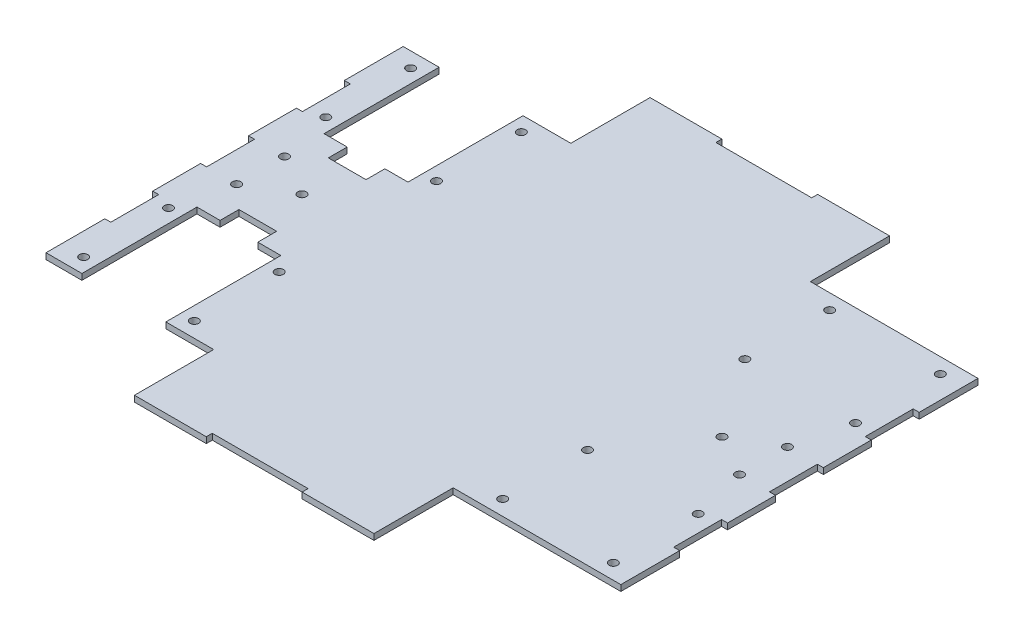
SolidWorks part; units mm, degrees
ref_plane "Front Plane" through (0, 0, 0) normal (0, 0, 1) x (1, 0, 0)
ref_plane "Top Plane" through (0, 0, 0) normal (0, 1, 0) x (1, 0, 0)
ref_plane "Right Plane" through (0, 0, 0) normal (1, 0, 0) x (0, 0, -1)
sketch "Sketch1" plane through (0, 0, 0) normal (0, 1, 0) x (1, 0, 0)
  line L0 (152.4, 94.7) -> (63.5, 94.7)
  line L1 (-152.4, -136.7) -> (152.4, -136.7)
  line L2 (-152.4, -136.7) -> (-152.4, 136.7)
  line L3 (-152.4, 136.7) -> (152.4, 136.7)
  line L4 (152.4, -136.7) -> (152.4, 136.7)
  line L5 (-152.4, -136.7) -> (152.4, 136.7) construction
  line L6 (-152.4, 136.7) -> (152.4, -136.7) construction
  line L7 (63.5, 94.7) -> (63.5, 136.7)
  line L8 (-152.4, 94.7) -> (-63.5, 94.7)
  line L9 (-63.5, 94.7) -> (-63.5, 136.7)
  line L10 (-152.4, -94.7) -> (-63.5, -94.7)
  line L11 (-63.5, -94.7) -> (-63.5, -136.7)
  line L12 (152.4, -94.7) -> (63.5, -94.7)
  line L13 (63.5, -94.7) -> (63.5, -136.7)
  line L14 (-88.8476, 33.7) -> (88.8476, 33.7) construction
  line L15 (88.8476, 33.7) -> (133.35, 33.7)
  line L16 (88.8476, 33.7) -> (88.8476, 94.7)
  line L17 (88.8476, 94.7) -> (133.35, 94.7)
  line L18 (133.35, 33.7) -> (133.35, 94.7)
  line L19 (88.8476, 33.7) -> (133.35, 94.7) construction
  line L20 (88.8476, 94.7) -> (133.35, 33.7) construction
  line L21 (88.8476, -33.7) -> (133.35, -33.7)
  line L22 (88.8476, -33.7) -> (88.8476, -94.7)
  line L23 (88.8476, -94.7) -> (133.35, -94.7)
  line L24 (133.35, -33.7) -> (133.35, -94.7)
  line L25 (88.8476, -33.7) -> (133.35, -94.7) construction
  line L26 (88.8476, -94.7) -> (133.35, -33.7) construction
  line L27 (-133.35, -33.7) -> (-88.8476, -33.7)
  line L28 (-133.35, -33.7) -> (-133.35, -94.7)
  line L29 (-133.35, -94.7) -> (-88.8476, -94.7)
  line L30 (-88.8476, -33.7) -> (-88.8476, -94.7)
  line L31 (-133.35, -33.7) -> (-88.8476, -94.7) construction
  line L32 (-133.35, -94.7) -> (-88.8476, -33.7) construction
  line L33 (-133.35, 33.7) -> (-88.8476, 33.7)
  line L34 (-133.35, 33.7) -> (-133.35, 94.7)
  line L35 (-133.35, 94.7) -> (-88.8476, 94.7)
  line L36 (-88.8476, 33.7) -> (-88.8476, 94.7)
  line L37 (-133.35, 33.7) -> (-88.8476, 94.7) construction
  line L38 (-133.35, 94.7) -> (-88.8476, 33.7) construction
  line L39 (-149.225, 38.1) -> (-149.225, 12.7) construction
  line L40 (152.4, 12.7) -> (149.225, 12.7)
  line L41 (152.4, 12.7) -> (152.4, -12.7)
  line L42 (152.4, -12.7) -> (149.225, -12.7)
  line L43 (149.225, 12.7) -> (149.225, -12.7)
  line L44 (152.4, 63.5) -> (149.225, 63.5)
  line L45 (152.4, 63.5) -> (152.4, 38.1)
  line L46 (152.4, 38.1) -> (149.225, 38.1)
  line L47 (149.225, 63.5) -> (149.225, 38.1)
  line L48 (152.4, -38.1) -> (149.225, -38.1)
  line L49 (152.4, -38.1) -> (152.4, -63.5)
  line L50 (152.4, -63.5) -> (149.225, -63.5)
  line L51 (149.225, -38.1) -> (149.225, -63.5)
  line L52 (-149.225, 63.5) -> (-152.4, 63.5)
  line L53 (-149.225, 63.5) -> (-149.225, 38.1)
  line L54 (-149.225, 38.1) -> (-152.4, 38.1)
  line L55 (-152.4, 63.5) -> (-152.4, 38.1)
  line L56 (-149.225, 12.7) -> (-152.4, 12.7)
  line L57 (-149.225, 12.7) -> (-149.225, -12.7)
  line L58 (-149.225, -12.7) -> (-152.4, -12.7)
  line L59 (-152.4, 12.7) -> (-152.4, -12.7)
  line L60 (-149.225, -38.1) -> (-152.4, -38.1)
  line L61 (-149.225, -38.1) -> (-149.225, -63.5)
  line L62 (-149.225, -63.5) -> (-152.4, -63.5)
  line L63 (-152.4, -38.1) -> (-152.4, -63.5)
  line L64 (-149.225, -12.7) -> (-149.225, -38.1) construction
  line L65 (149.225, 38.1) -> (149.225, 12.7) construction
  line L66 (149.225, -12.7) -> (149.225, -38.1) construction
  line L67 (133.35, -12.7) -> (133.35, 12.7) construction
  line L68 (25.4, -136.7) -> (-25.4, -136.7)
  line L69 (25.4, -136.7) -> (25.4, -133.525)
  line L70 (25.4, -133.525) -> (-25.4, -133.525)
  line L71 (-25.4, -136.7) -> (-25.4, -133.525)
  line L72 (25.4, 136.7) -> (-25.4, 136.7)
  line L73 (25.4, 136.7) -> (25.4, 133.525)
  line L74 (25.4, 133.525) -> (-25.4, 133.525)
  line L75 (-25.4, 136.7) -> (-25.4, 133.525)
  line L76 (133.35, -12.7) -> (111.353, 0) construction
  line L77 (111.353, 0) -> (133.35, 12.7) construction
  line L78 (-133.35, -12.7) -> (-133.35, 12.7) construction
  line L79 (81.7565, 41.7) -> (140.4411, 41.7) construction
  line L80 (81.7565, 41.7) -> (81.7565, 86.7) construction
  line L81 (81.7565, 86.7) -> (140.4411, 86.7) construction
  line L82 (140.4411, 41.7) -> (140.4411, 86.7) construction
  line L83 (81.7565, 41.7) -> (140.4411, 86.7) construction
  line L84 (81.7565, 86.7) -> (140.4411, 41.7) construction
  line L85 (81.7565, -86.7) -> (140.4411, -86.7) construction
  line L86 (81.7565, -86.7) -> (81.7565, -41.7) construction
  line L87 (81.7565, -41.7) -> (140.4411, -41.7) construction
  line L88 (140.4411, -86.7) -> (140.4411, -41.7) construction
  line L89 (81.7565, -86.7) -> (140.4411, -41.7) construction
  line L90 (81.7565, -41.7) -> (140.4411, -86.7) construction
  line L91 (-140.4411, -86.7) -> (-81.7565, -86.7) construction
  line L92 (-140.4411, -86.7) -> (-140.4411, -41.7) construction
  line L93 (-140.4411, -41.7) -> (-81.7565, -41.7) construction
  line L94 (-81.7565, -86.7) -> (-81.7565, -41.7) construction
  line L95 (-140.4411, -86.7) -> (-81.7565, -41.7) construction
  line L96 (-140.4411, -41.7) -> (-81.7565, -86.7) construction
  line L97 (-140.4411, 41.7) -> (-81.7565, 41.7) construction
  line L98 (-140.4411, 41.7) -> (-140.4411, 86.7) construction
  line L99 (-140.4411, 86.7) -> (-81.7565, 86.7) construction
  line L100 (-81.7565, 41.7) -> (-81.7565, 86.7) construction
  line L101 (-140.4411, 41.7) -> (-81.7565, 86.7) construction
  line L102 (-140.4411, 86.7) -> (-81.7565, 41.7) construction
  line L103 (-133.35, 12.7) -> (-111.353, 0) construction
  line L104 (-111.353, 0) -> (-133.35, -12.7) construction
  line L106 (-121.0988, 23.7) -> (-101.0988, 23.7)
  line L107 (-121.0988, 23.7) -> (-121.0988, 33.7)
  line L108 (-121.0988, 33.7) -> (-101.0988, 33.7)
  line L109 (-101.0988, 23.7) -> (-101.0988, 33.7)
  line L110 (-121.0988, 23.7) -> (-101.0988, 33.7) construction
  line L111 (-121.0988, 33.7) -> (-101.0988, 23.7) construction
  line L112 (-121.0988, -23.7) -> (-101.0988, -23.7)
  line L113 (-121.0988, -23.7) -> (-121.0988, -33.7)
  line L114 (-121.0988, -33.7) -> (-101.0988, -33.7)
  line L115 (-101.0988, -23.7) -> (-101.0988, -33.7)
  line L116 (-121.0988, -23.7) -> (-101.0988, -33.7) construction
  line L117 (-121.0988, -33.7) -> (-101.0988, -23.7) construction
  line L118 (101.0988, -23.7) -> (121.0988, -23.7)
  line L119 (101.0988, -23.7) -> (101.0988, -33.7)
  line L120 (101.0988, -33.7) -> (121.0988, -33.7)
  line L121 (121.0988, -23.7) -> (121.0988, -33.7)
  line L122 (101.0988, -23.7) -> (121.0988, -33.7) construction
  line L123 (101.0988, -33.7) -> (121.0988, -23.7) construction
  line L124 (101.0988, 23.7) -> (121.0988, 23.7)
  line L125 (101.0988, 23.7) -> (101.0988, 33.7)
  line L126 (101.0988, 33.7) -> (121.0988, 33.7)
  line L127 (121.0988, 23.7) -> (121.0988, 33.7)
  line L128 (101.0988, 23.7) -> (121.0988, 33.7) construction
  line L129 (101.0988, 33.7) -> (121.0988, 23.7) construction
  circle A0 centre (133.35, -12.7) radius 2.25
  circle A1 centre (133.35, 12.7) radius 2.25
  circle A2 centre (111.353, 0) radius 2.25
  circle A3 centre (-81.7565, 41.7) radius 2.25
  circle A4 centre (-81.7565, 86.7) radius 2.25
  circle A5 centre (-140.4411, 86.7) radius 2.25
  circle A6 centre (-140.4411, 41.7) radius 2.25
  circle A7 centre (-81.7565, -41.7) radius 2.25
  circle A8 centre (-81.7565, -86.7) radius 2.25
  circle A9 centre (-140.4411, -86.7) radius 2.25
  circle A10 centre (-140.4411, -41.7) radius 2.25
  circle A11 centre (81.7565, -41.7) radius 2.25
  circle A12 centre (81.7565, -86.7) radius 2.25
  circle A13 centre (140.4411, -41.7) radius 2.25
  circle A14 centre (140.4411, -86.7) radius 2.25
  circle A15 centre (81.7565, 41.7) radius 2.25
  circle A16 centre (81.7565, 86.7) radius 2.25
  circle A17 centre (140.4411, 86.7) radius 2.25
  circle A18 centre (140.4411, 41.7) radius 2.25
  circle A19 centre (-133.35, -12.7) radius 2.25
  circle A20 centre (-133.35, 12.7) radius 2.25
  circle A21 centre (-111.353, 0) radius 2.25
  point P0 (0, 0)
  point P18 (111.0988, 64.2)
  point P23 (111.0988, -64.2)
  point P28 (-111.0988, -64.2)
  point P33 (-111.0988, 64.2)
  point P38 (0, 33.7)
  point P43 (149.225, 0)
  point P68 (0, -133.525)
  point P79 (111.0988, 64.2)
  point P80 (133.35, 0)
  point P85 (111.0988, -64.2)
  point P90 (-111.0988, -64.2)
  point P95 (-111.0988, 64.2)
  point P122 (-111.0988, 28.7)
  point P123 (-133.35, 0)
  point P128 (-111.0988, -28.7)
  point P133 (111.0988, -28.7)
  point P138 (111.0988, 28.7)
  point P143 (0, 0)
  point P144 (0, 0)
  dimension "D12" = 4.5
  dimension "D14" = 45
  dimension "D16" = 4.5
  dimension "D1" = 304.8
  dimension "D2" = 273.4
  dimension "D3" = 42
  dimension "D4" = 88.9
  dimension "D5" = 61
  dimension "D6" = 44.5024
  dimension "D7" = 19.05
  dimension "D8" = 25.4
  dimension "D9" = 3.175
  dimension "D10" = 50.8
  dimension "D11" = 3.175
  dimension "D13" = 25.4
  dimension "D15" = 58.6846
  dimension "D17" = 10
  dimension "D18" = 20
extrude "Boss-Extrude1" add sketch "Sketch1" along normal blind 3.175 contours L13 L12 L4 L0 L7 L3 L9 L8 L2 L10 L11 L1 | L15 L18 L0 L16 | L124 L127 L15 L125 | L121 L118 L119 L21 | L24 L21 L22 L12 | A14 | A13
